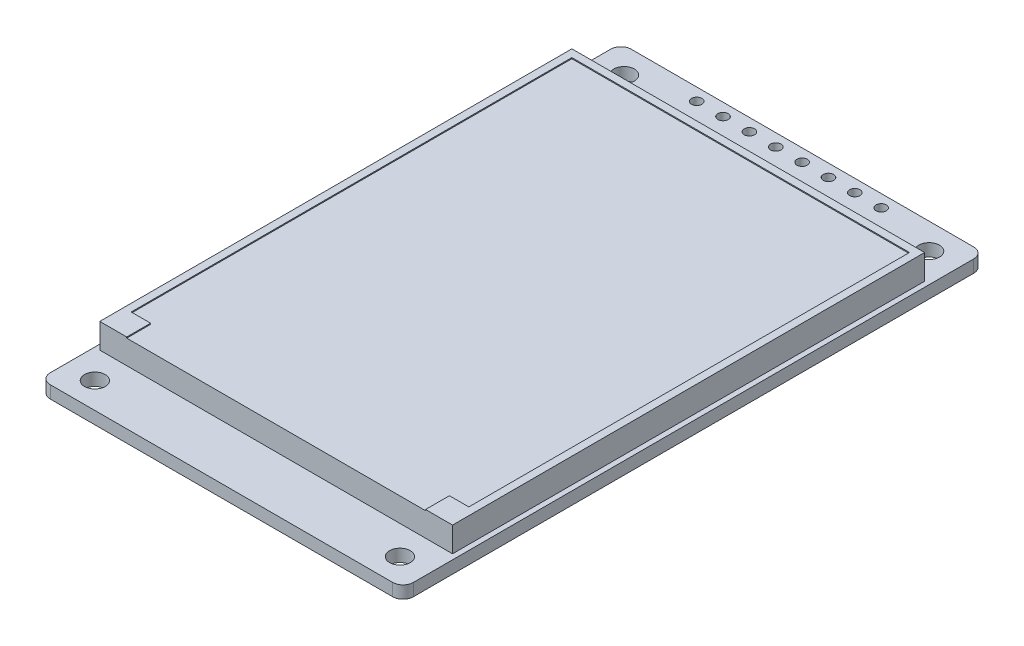
SolidWorks part; units mm, degrees
ref_plane "Front Plane" through (0, 0, 0) normal (0, 0, 1) x (1, 0, 0)
ref_plane "Top Plane" through (0, 0, 0) normal (0, 1, 0) x (1, 0, 0)
ref_plane "Right Plane" through (0, 0, 0) normal (1, 0, 0) x (0, 0, -1)
sketch "Sketch1" plane through (0, 0, 0) normal (0, 1, 0) x (1, 0, 0)
  line L0 (0, 28) -> (0, -28) construction
  line L1 (-17.5, -28) -> (17.5, -28)
  line L2 (-17.5, -28) -> (-17.5, 28)
  line L3 (-17.5, 28) -> (17.5, 28)
  line L4 (17.5, -28) -> (17.5, 28)
  line L5 (-17.5, -28) -> (17.5, 28) construction
  line L6 (-17.5, 28) -> (17.5, -28) construction
  line L7 (-17.5, 0) -> (17.5, 0) construction
  circle A0 centre (-14.7, 25.5) radius 1
  circle A1 centre (14.7, 25.5) radius 1
  circle A2 centre (-14.7, -25.5) radius 1
  circle A3 centre (14.7, -25.5) radius 1
  circle A4 centre (-9, 26.8) radius 0.5
  circle A5 centre (-6.46, 26.8) radius 0.5
  circle A6 centre (-3.92, 26.8) radius 0.5
  circle A7 centre (-1.38, 26.8) radius 0.5
  circle A8 centre (1.16, 26.8) radius 0.5
  circle A9 centre (3.7, 26.8) radius 0.5
  circle A10 centre (6.24, 26.8) radius 0.5
  circle A11 centre (8.78, 26.8) radius 0.5
  point P0 (0, 0)
  dimension "D3" = 2
  dimension "D4" = 2.8
  dimension "D5" = 2.5
  dimension "D6" = 1.2
  dimension "D7" = 1
  dimension "D8" = 8.5
  dimension "D1" = 35
  dimension "D2" = 56
  dimension "D9" = 8
extrude "Boss-Extrude1" add sketch "Sketch1" along normal blind 1.2
fillet "Fillet1" radius 1 4 edges at (-17.5, 0.6, -28) (17.5, 0.6, -28) (-17.5, 0.6, 28) (17.5, 0.6, 28)
sketch "Sketch2" plane through (0, 1.2, 0) normal (0, 1, 0) x (1, 0, 0)
  line L0 (-17.5, 27) -> (-17.5, -27) construction
  line L1 (-17, -22.73) -> (17, -22.73)
  line L2 (-17, -22.73) -> (-17, 22.77)
  line L3 (-17, 22.77) -> (17, 22.77)
  line L4 (17, -22.73) -> (17, 22.77)
  line L5 (-17, -22.73) -> (17, 22.77) construction
  line L6 (-17, 22.77) -> (17, -22.73) construction
  line L7 (16.5, 28) -> (-16.5, 28) construction
  point P0 (0, 0.02)
  dimension "D1" = 34
  dimension "D2" = 45.5
  dimension "D3" = 0.5
  dimension "D4" = 5.23
extrude "Boss-Extrude2" add sketch "Sketch2" along normal blind 2.4
sketch "Sketch3" plane through (0, 3.6, 0) normal (0, 1, 0) x (1, 0, 0)
  line L0 (-17, 22.77) -> (-17, -22.73) construction
  line L1 (-16.27, 22.04) -> (16.27, 22.04)
  line L2 (-16.27, 22.04) -> (-16.27, -20.43)
  line L3 (-16.27, -20.43) -> (-14.4, -20.43)
  line L4 (16.27, 22.04) -> (16.27, -20.43)
  line L5 (17, -22.73) -> (17, 22.77) construction
  line L6 (17, 22.77) -> (-17, 22.77) construction
  line L7 (-17, -22.73) -> (17, -22.73) construction
  line L8 (-17, -22.73) -> (17, -22.73) construction
  line L10 (-14.4, -20.43) -> (-14.4, -22.73)
  line L11 (-14.4, -22.73) -> (14.4, -22.73)
  line L12 (14.4, -20.43) -> (14.4, -22.73)
  line L13 (14.4, -20.43) -> (16.27, -20.43)
  point P16 (0, -22.73)
  point P19 (0, -22.73)
  dimension "D1" = 0.73
  dimension "D2" = 0.73
  dimension "D3" = 0.73
  dimension "D4" = 2.3
  dimension "D5" = 28.8
extrude "Cut-Extrude1" cut sketch "Sketch3" against normal blind 0.1
